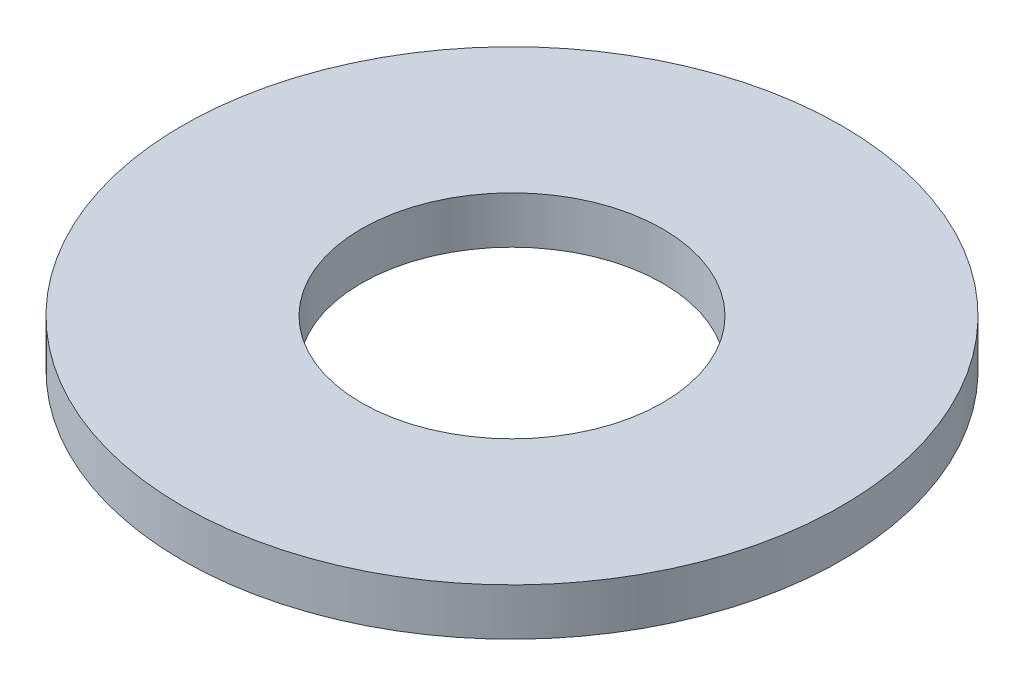
SolidWorks part; units mm, degrees
material "Plain Carbon Steel"
ref_plane "Front Plane" through (0, 0, 0) normal (0, 0, 1) x (1, 0, 0)
ref_plane "Top Plane" through (0, 0, 0) normal (0, 1, 0) x (1, 0, 0)
ref_plane "Right Plane" through (0, 0, 0) normal (1, 0, 0) x (0, 0, -1)
sketch "Sketch1" plane through (0, 0, 0) normal (0, 1, 0) x (1, 0, 0)
  circle A0 centre (0, 0) radius 1.6
  circle A1 centre (0, 0) radius 3.5
  dimension "D1" = 3.2
  dimension "D2" = 7
extrude "Extrude1" add sketch "Sketch1" along normal blind 0.5
